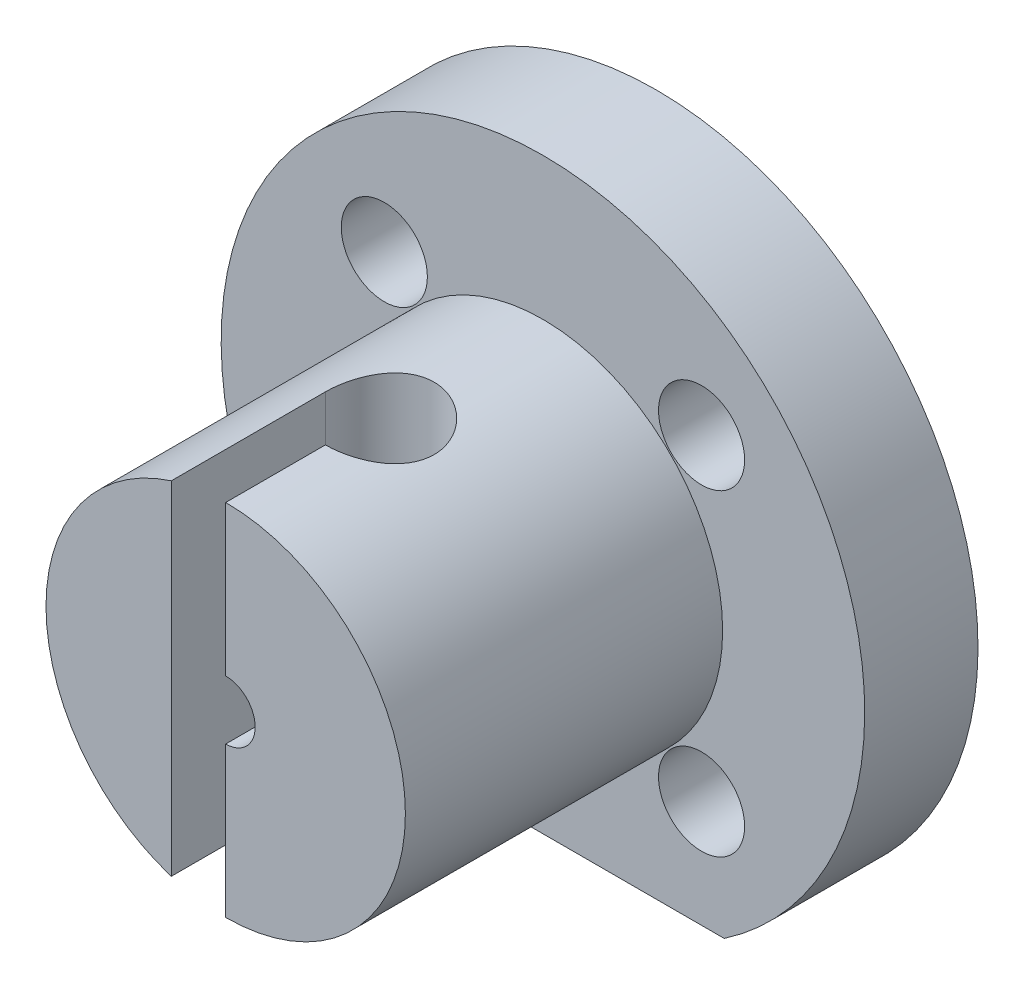
SolidWorks part; units mm, degrees
ref_plane "Alzado" through (0, 0, 0) normal (0, 0, 1) x (1, 0, 0)
ref_plane "Planta" through (0, 0, 0) normal (0, 1, 0) x (1, 0, 0)
ref_plane "Vista lateral" through (0, 0, 0) normal (1, 0, 0) x (0, 0, -1)
sketch "Croquis1" plane through (0, 0, 0) normal (0, 0, 1) x (1, 0, 0)
  line L0 (0, 0) -> (61.4595, 0) construction
  circle A5 centre (0, 0) radius 35.5
  circle A6 centre (0, 0) radius 3.25
  point P16 (0, 0)
  dimension "D6" = 71
  dimension "D7" = 6.5
extrude "Saliente-Extruir1" add sketch "Croquis1" along normal blind 5
sketch "Croquis9" plane through (0, 0, 5) normal (0, 0, 1) x (1, 0, 0)
  circle A0 centre (0, 0) radius 19.825
  circle A1 centre (0, 0) radius 3.25
  dimension "D1" = 39.65
extrude "Saliente-Extruir4" add sketch "Croquis9" along normal blind 35
sketch "Croquis10" plane through (0, 0, 0) normal (0, 1, 0) x (1, 0, 0)
  line L0 (0, -23) -> (0, -29) construction
  line L1 (-19.825, -40) -> (19.825, -40) construction
  line L2 (0, -29) -> (0, -40)
  line L3 (-3.25, -40) -> (3.25, -40) construction
  line L4 (0, -40) -> (-6, -40)
  line L5 (-6, -40) -> (-6, -23)
  arc A0 (0, -29) -> (-6, -23) centre (0, -23) ccw
  dimension "D2" = 6
  dimension "D1" = 17
extrude "Cortar-Extruir4" cut sketch "Croquis10" against normal through all both and the other way through all
sketch "Croquis11" plane through (0, 0, 0) normal (0, 0, -1) x (-1, 0, 0)
  circle A1 centre (0, 0) radius 35.5
  circle A2 centre (0, 0) radius 35.5
  circle A3 centre (0, 0) radius 3.25 construction
  circle A8 centre (0, 0) radius 3.25
  dimension "D1" = 0
extrude "Saliente-Extruir5" add sketch "Croquis11" along normal blind 7.5
sketch "Croquis13" plane through (0, 0, 5) normal (0, 0, 1) x (1, 0, 0)
  line L1 (-20, -29.33) -> (20, -29.33)
  circle A6 centre (0, 0) radius 35.5 construction
  arc A7 (-20, -29.33) -> (20, -29.33) centre (0, 0) ccw
  arc A8 (20, -29.33) -> (-20, -29.33) centre (0, 0) ccw construction
  point P12 (0, 0)
  dimension "D5" = 40
extrude "Cortar-Extruir5" cut sketch "Croquis13" against normal blind 7.5
sketch "Croquis15" plane through (0, 0, 5) normal (0, 0, 1) x (1, 0, 0)
  line L1 (20, -29.33) -> (-20, -29.33)
  line L2 (20, -29.33) -> (-20, -29.33)
  arc A1 (-20, -29.33) -> (20, -29.33) centre (0, 0) ccw
  arc A2 (-20, -29.33) -> (20, -29.33) centre (0, 0) ccw
  dimension "D1" = 0
extrude "Cortar-Extruir7" cut sketch "Croquis15" against normal through all
sketch "Croquis16" plane through (0, 0, -7.5) normal (0, 0, -1) x (-1, 0, 0)
  circle A0 centre (17.5009, -17.5009) radius 4.75
  circle A1 centre (0, 0) radius 24.75 construction
  circle A2 centre (-17.5009, -17.5009) radius 4.75
  circle A3 centre (0, 0) radius 24.75 construction
  circle A4 centre (-17.5009, 17.5009) radius 4.75
  circle A5 centre (0, 0) radius 24.75 construction
  circle A6 centre (17.5009, 17.5009) radius 4.75
  circle A7 centre (0, 0) radius 24.75 construction
  point P18 (0, 0)
  dimension "D1" = 9.5
  dimension "D2" = 4
extrude "Cortar-Extruir8" cut sketch "Croquis16" against normal up to next
